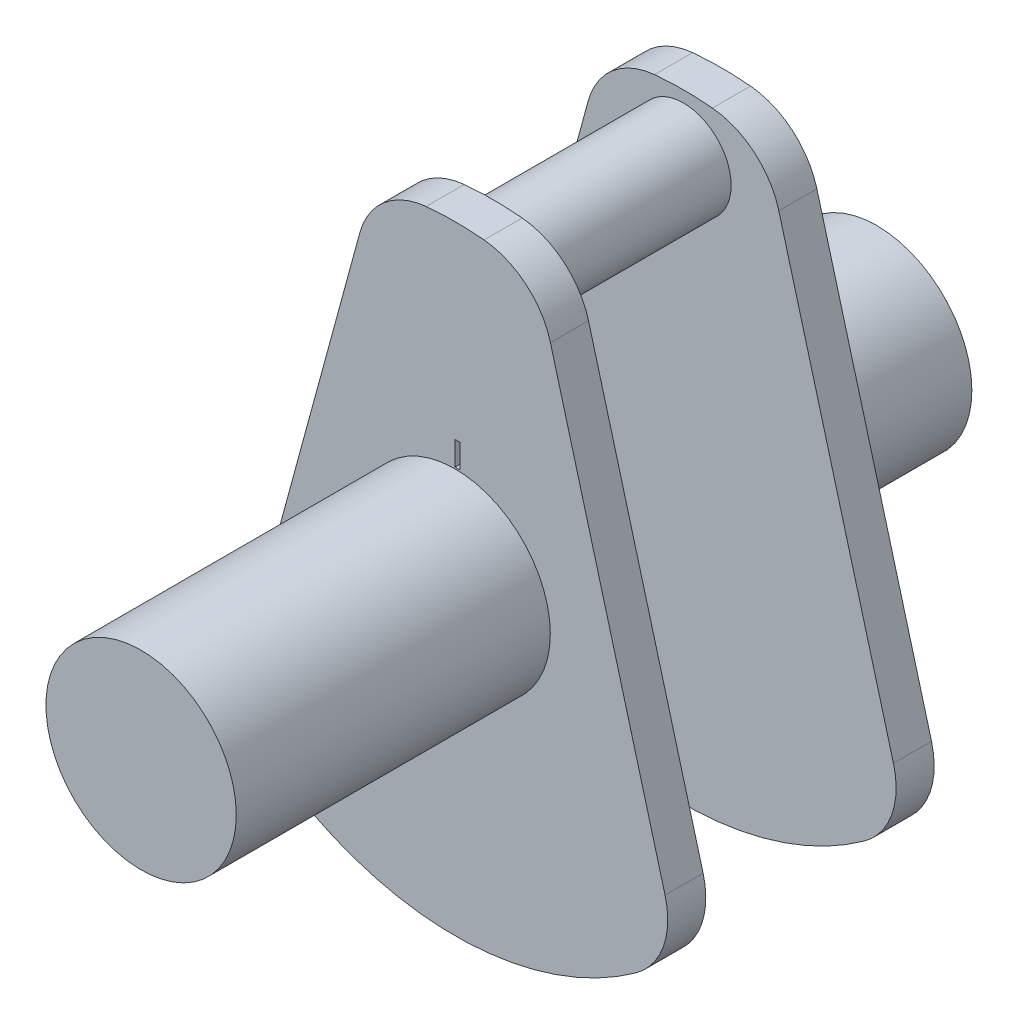
SolidWorks part; units mm, degrees
ref_plane "Front Plane" through (0, 0, 0) normal (0, 0, 1) x (1, 0, 0)
ref_plane "Top Plane" through (0, 0, 0) normal (0, 1, 0) x (1, 0, 0)
ref_plane "Right Plane" through (0, 0, 0) normal (1, 0, 0) x (0, 0, -1)
sketch "Sketch1" plane through (0, 0, 0) normal (0, 0, 1) x (1, 0, 0)
  line L0 (0, 6.5) -> (0, -6.5) construction
  line L1 (-2.0028, 5.2986) -> (-4.4119, -3.5528)
  line L2 (2.0028, 5.2986) -> (4.4119, -3.5528)
  arc A0 (-3.8045, -5.2703) -> (3.8045, -5.2703) centre (0, 0) ccw
  arc A1 (0.6089, 6.4714) -> (-0.6089, 6.4714) centre (0, 0) ccw
  arc A2 (2.0028, 5.2986) -> (0.6089, 6.4714) centre (0.459, 4.8785) ccw
  arc A3 (-2.0028, 5.2986) -> (-0.6089, 6.4714) centre (-0.459, 4.8785) cw
  arc A4 (4.4119, -3.5528) -> (3.8045, -5.2703) centre (2.868, -3.973) cw
  arc A5 (-4.4119, -3.5528) -> (-3.8045, -5.2703) centre (-2.868, -3.973) ccw
  point P10 (1.7405, 6.2626)
  point P13 (-1.7405, 6.2626)
  point P16 (4.6742, -4.5168)
  point P19 (-4.6742, -4.5168)
  dimension "D1" = 13
  dimension "D4" = 1.6
  dimension "D5" = 1.6
  dimension "D2" = 30.45
  dimension "D3" = 0.918
extrude "Boss-Extrude1" add sketch "Sketch1" along normal blind 0.8
sketch "Sketch2" plane through (0, 0, 0.8) normal (0, 0, 1) x (1, 0, 0)
  line L0 (0, 6.5) -> (0, 5.259) construction
  arc A0 (0.6089, 6.4714) -> (-0.6089, 6.4714) centre (0, 0) ccw construction
  circle A1 centre (0, 5.259) radius 1
  dimension "D1" = 2
  dimension "D2" = 5.259
extrude "Boss-Extrude2" add sketch "Sketch2" along normal blind 2
sketch "Sketch3" plane through (0, 0, 0) normal (0, 0, -1) x (-1, 0, 0)
  circle A0 centre (0, 0) radius 2
  dimension "D1" = 4
extrude "Boss-Extrude3" add sketch "Sketch3" along normal blind 3.26
mirror "Mirror3" about plane through (0, 5.259, 2.8) normal (0, 0, 1) of bodies 103
sketch "Sketch4" plane through (0, 0, 8.86) normal (0, 0, 1) x (1, 0, 0)
  circle A1 centre (0, 0) radius 2
  circle A2 centre (0, 0) radius 2
  dimension "D1" = 0
extrude "Boss-Extrude4" add sketch "Sketch4" along normal blind 3.34
sketch "Sketch6" plane through (0, 0, 5.6) normal (0, 0, 1) x (1, 0, 0)
  line L0 (0, 5.2796) -> (0, 0) construction
  line L2 (0, 2.5333) -> (0.1, 2.5333)
  line L3 (0, 2.5333) -> (0, 2.0333)
  line L4 (0, 2.0333) -> (0.1, 2.0333)
  line L5 (0.1, 2.5333) -> (0.1, 2.0333)
  dimension "D1" = 0.1
  dimension "D2" = 0.5
extrude "Cut-Extrude2" cut sketch "Sketch6" against normal blind 0.1 contours L3 L2 L5 L4
